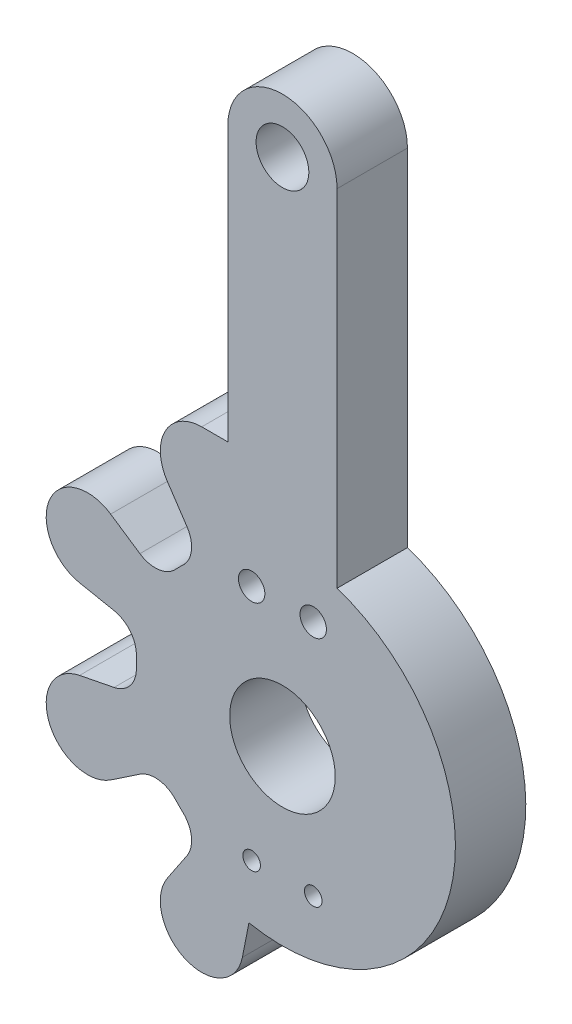
SolidWorks part; units mm, degrees
material "Beech"
ref_plane "Front Plane" through (0, 0, 0) normal (0, 0, 1) x (1, 0, 0)
ref_plane "Top Plane" through (0, 0, 0) normal (0, 1, 0) x (1, 0, 0)
ref_plane "Right Plane" through (0, 0, 0) normal (1, 0, 0) x (0, 0, -1)
sketch "Sketch1" plane through (0, 0, 0) normal (0, 0, 1) x (1, 0, 0)
  line L0 (16.5306, 42.4256) -> (16.5306, 22.755)
  line L1 (10.3206, 42.4256) -> (10.3206, 26.8556)
  line L2 (11.1471, 1.8933) -> (11.5198, 3.7796)
  line L3 (7.996, 5.3221) -> (6.8822, 3.6599)
  line L4 (3.6599, 6.8822) -> (5.3221, 7.9959)
  line L5 (3.8562, 11.5349) -> (1.8933, 11.1471)
  line L6 (1.8933, 15.7041) -> (3.8562, 15.3163)
  line L7 (5.3221, 18.8553) -> (3.6599, 19.969)
  line L8 (6.8822, 23.1913) -> (7.996, 21.5292)
  line L9 (8.8378, 26.8556) -> (10.3206, 26.8556)
  arc A0 (11.0948, 1.6811) -> (11.1471, 1.8933) centre (8.8378, 2.3496) ccw
  arc A1 (6.8822, 3.6599) -> (6.7691, 3.4728) centre (8.8378, 2.3496) ccw
  arc A2 (7.996, 5.3221) -> (7.7618, 7.344) centre (6.6922, 6.1956) ccw
  arc A3 (7.344, 7.7618) -> (7.7618, 7.344) centre (13.4256, 13.4256) ccw
  arc A4 (7.344, 7.7618) -> (5.3221, 7.9959) centre (6.1956, 6.6922) ccw
  arc A5 (3.4728, 6.7691) -> (3.6599, 6.8822) centre (2.3496, 8.8378) ccw
  arc A6 (1.8933, 11.1471) -> (1.6811, 11.0948) centre (2.3496, 8.8378) ccw
  arc A7 (3.8562, 11.5349) -> (5.1203, 13.1302) centre (3.552, 13.0745) ccw
  arc A8 (5.1203, 13.721) -> (5.1203, 13.1302) centre (13.4256, 13.4256) ccw
  arc A9 (5.1203, 13.721) -> (3.8562, 15.3163) centre (3.552, 13.7768) ccw
  arc A10 (1.6811, 15.7564) -> (1.8933, 15.7041) centre (2.3496, 18.0135) ccw
  arc A11 (3.6599, 19.969) -> (3.4728, 20.0821) centre (2.3496, 18.0135) ccw
  arc A12 (5.3221, 18.8553) -> (7.344, 19.0895) centre (6.1956, 20.159) ccw
  arc A13 (7.7618, 19.5072) -> (7.344, 19.0895) centre (13.4256, 13.4256) ccw
  arc A14 (7.7618, 19.5072) -> (7.996, 21.5292) centre (6.6922, 20.6556) ccw
  arc A15 (6.7691, 23.3784) -> (6.8822, 23.1913) centre (8.8378, 24.5016) ccw
  arc A16 (6.7549, 3.4463) -> (11.0861, 1.6522) centre (8.8378, 2.3496) ccw
  arc A17 (3.4463, 20.0963) -> (1.6522, 15.7652) centre (2.3496, 18.0135) ccw
  arc A18 (1.6522, 11.0861) -> (3.4463, 6.7549) centre (2.3496, 8.8378) ccw
  arc A19 (8.8378, 26.8556) -> (6.7549, 23.405) centre (8.8378, 24.5016) ccw
  arc A20 (1.6811, 11.0948) -> (1.6522, 11.0861) centre (2.3496, 8.8378) ccw
  arc A21 (3.4463, 6.7549) -> (3.4728, 6.7691) centre (2.3496, 8.8378) ccw
  arc A22 (6.7691, 3.4728) -> (6.7549, 3.4463) centre (8.8378, 2.3496) ccw
  arc A23 (11.0861, 1.6522) -> (11.0948, 1.6811) centre (8.8378, 2.3496) ccw
  arc A24 (6.7549, 23.405) -> (6.7691, 23.3784) centre (8.8378, 24.5016) ccw
  arc A25 (3.4728, 20.0821) -> (3.4463, 20.0963) centre (2.3496, 18.0135) ccw
  arc A26 (1.6522, 15.7652) -> (1.6811, 15.7564) centre (2.3496, 18.0135) ccw
  arc A27 (11.5198, 3.7796) -> (16.5306, 22.755) centre (13.4256, 13.4256) ccw
  circle A28 centre (13.4256, 42.4256) radius 1.5
  arc A29 (16.5306, 42.4256) -> (10.3206, 42.4256) centre (13.4256, 42.4256) ccw
  circle A30 centre (13.4256, 13.4256) radius 3
  circle A31 centre (11.6756, 20.4256) radius 0.75
  circle A32 centre (15.1756, 20.4256) radius 0.75
  circle A33 centre (11.6756, 6.9256) radius 0.5
  circle A34 centre (15.1756, 6.9256) radius 0.5
extrude "Boss-Extrude1" add sketch "Sketch1" along normal blind 4
